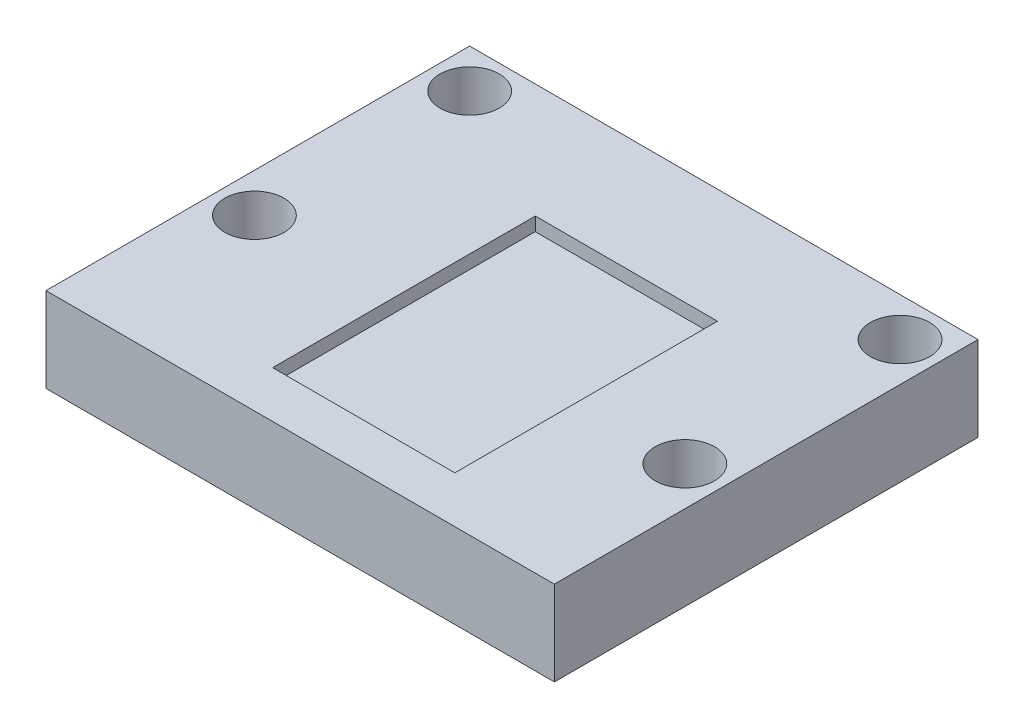
SolidWorks part; units mm, degrees
ref_plane "Front Plane" through (0, 0, 0) normal (0, 0, 1) x (1, 0, 0)
ref_plane "Top Plane" through (0, 0, 0) normal (0, 1, 0) x (1, 0, 0)
ref_plane "Right Plane" through (0, 0, 0) normal (1, 0, 0) x (0, 0, -1)
sketch "Sketch2" plane through (0, 0, 0) normal (0, 1, 0) x (1, 0, 0)
  line L1 (0, 0) -> (60, 0)
  line L2 (0, 0) -> (0, 50)
  line L3 (0, 50) -> (60, 50)
  line L4 (60, 0) -> (60, 50)
  dimension "D1" = 50
  dimension "D2" = 60
extrude "Boss-Extrude1" add sketch "Sketch2" along normal blind 10
sketch "Sketch1" plane through (0, 10, 0) normal (0, 1, 0) x (1, 0, 0)
  line L0 (60, 50) -> (0, 50) construction
  line L5 (4.6, 45.4) -> (55.4, 45.4) construction
  line L6 (4.6, 45.4) -> (4.6, 20) construction
  line L7 (4.6, 20) -> (55.4, 20) construction
  line L8 (55.4, 45.4) -> (55.4, 20) construction
  line L10 (4.6, 45.4) -> (0, 45.4)
  line L11 (0, 50) -> (0, 0) construction
  line L12 (4.6, 45.4) -> (4.6, 50)
  circle A0 centre (4.6, 20) radius 3.5
  circle A1 centre (4.6, 45.4) radius 3.5
  circle A2 centre (55.4, 45.4) radius 3.5
  circle A3 centre (55.4, 20) radius 3.5
  point P2 (30, 50)
  point P3 (30, 45.4)
  dimension "D5" = 7
  dimension "D3" = 25.4
  dimension "D4" = 50.8
extrude "Cut-Extrude1" cut sketch "Sketch1" against normal blind 10 contours L12 A1 L10 | L10 A1 L12 | A2 | A0 | A3
sketch "Sketch3" plane through (0, 10, 0) normal (0, 1, 0) x (1, 0, 0)
  line L0 (60, 50) -> (0, 50) construction
  line L1 (21.25, 36.5) -> (42.75, 36.5)
  line L2 (21.25, 36.5) -> (21.25, 5.5)
  line L3 (21.25, 5.5) -> (42.75, 5.5)
  line L4 (42.75, 36.5) -> (42.75, 5.5)
  circle A0 centre (30, 32.5) radius 2.25 construction
  point P9 (30, 50)
  dimension "D4" = 4.5
  dimension "D1" = 21.5
  dimension "D2" = 31
  dimension "D3" = 4
  dimension "D5" = 8.75
  dimension "D6" = 17.5
extrude "Cut-Extrude2" cut sketch "Sketch3" against normal blind 1.6
